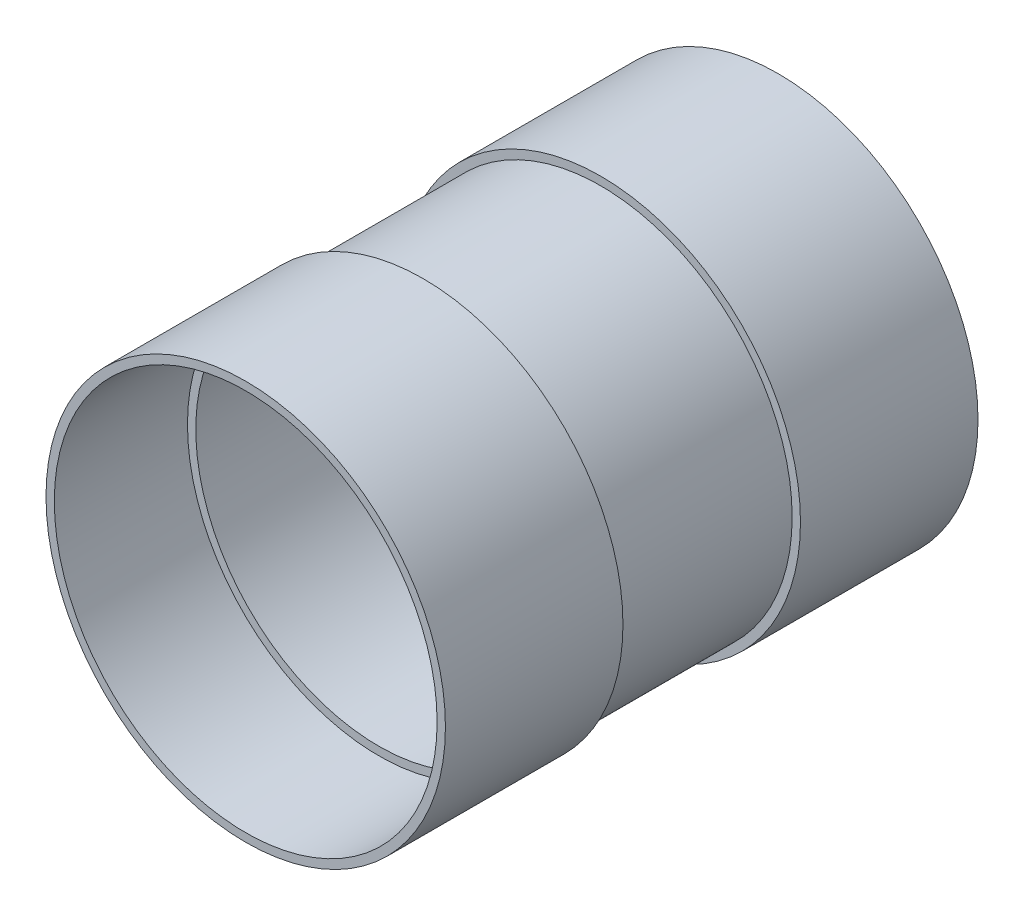
SolidWorks part; units mm, degrees
ref_plane "Front" through (0, 0, 0) normal (0, 0, 1) x (1, 0, 0)
ref_plane "Top" through (0, 0, 0) normal (0, 1, 0) x (1, 0, 0)
ref_plane "Right" through (0, 0, 0) normal (1, 0, 0) x (0, 0, -1)
sketch "Sketch2" plane through (0, 0, 0) normal (1, 0, 0) x (0, 0, -1)
  line L0 (-62.5946, 0) -> (53.5645, 0) construction
  line L1 (-152.4, 114.3) -> (-50.8, 114.3)
  line L2 (-50.8, 114.3) -> (-50.8, 109.5375)
  line L7 (-50.8, 109.5375) -> (-152.4, 109.5375)
  line L8 (-152.4, 109.5375) -> (-152.4, 114.3)
  line L9 (0, 0) -> (0, 72.5353) construction
  line L11 (50.8, 114.3) -> (152.4, 114.3)
  line L12 (50.8, 114.3) -> (50.8, 109.5375)
  line L13 (50.8, 109.5375) -> (152.4, 109.5375)
  line L14 (152.4, 114.3) -> (152.4, 109.5375)
  point P13 (152.4, 111.9188)
  dimension "D1" = 101.6
  dimension "D2" = 4.7625
  dimension "D3" = 304.8
  dimension "D4" = 219.075
revolve "Revolve1" add sketch "Sketch2" angle 360 about L0
sketch "Sketch3" plane through (0, 0, 0) normal (1, 0, 0) x (0, 0, -1)
  line L1 (-76.2, 104.775) -> (76.2, 104.775)
  line L2 (-76.2, 104.775) -> (-76.2, 109.5375)
  line L3 (-76.2, 109.5375) -> (76.2, 109.5375)
  line L4 (76.2, 104.775) -> (76.2, 109.5375)
  line L6 (0, 0) -> (103.0496, 0) construction
  line L7 (-50.8, 109.5375) -> (-152.4, 109.5375) construction
  line L8 (-152.4, 114.3) -> (-152.4, -114.3) construction
  line L9 (152.4, -114.3) -> (152.4, 114.3) construction
  point P4 (0, 0)
  point P5 (-86.0742, 109.5375)
  point P6 (0, 0)
  dimension "D1" = 4.7625
  dimension "D2" = 76.2
  dimension "D3" = 76.2
revolve "Revolve2" add sketch "Sketch3" angle 360 about L6
